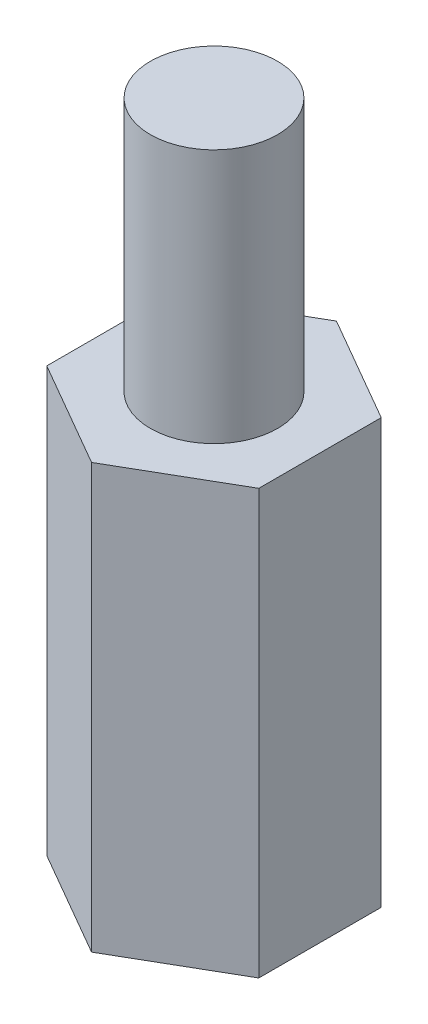
SolidWorks part; units mm, degrees
material "1023 Carbon Steel Sheet (SS)"
ref_plane "Front Plane" through (0, 0, 0) normal (0, 0, 1) x (1, 0, 0)
ref_plane "Top Plane" through (0, 0, 0) normal (0, 1, 0) x (1, 0, 0)
ref_plane "Right Plane" through (0, 0, 0) normal (1, 0, 0) x (0, 0, -1)
sketch "Sketch1" plane through (0, 0, 0) normal (0, 1, 0) x (1, 0, 0)
  line L1 (2.5, 1.4434) -> (0, 2.8868)
  line L2 (0, 2.8868) -> (-2.5, 1.4434)
  line L3 (-2.5, 1.4434) -> (-2.5, -1.4434)
  line L4 (-2.5, -1.4434) -> (0, -2.8868)
  line L5 (0, -2.8868) -> (2.5, -1.4434)
  line L6 (2.5, -1.4434) -> (2.5, 1.4434)
  circle A0 centre (0, 0) radius 2.5 construction
  dimension "D1" = 5
extrude "Boss-Extrude1" add sketch "Sketch1" along normal blind 16
sketch "Sketch2" plane through (0, 0, 0) normal (0, 1, 0) x (1, 0, 0)
  circle A0 centre (0, 0) radius 1.5025
  dimension "D1" = 3.005
extrude "Cut-Extrude1" cut sketch "Sketch2" along normal blind 6.005
sketch "Sketch3" plane through (0, 16, 0) normal (0, 1, 0) x (1, 0, 0)
  line L1 (0, 2.8868) -> (-2.5, 1.4434)
  line L2 (-2.5, 1.4434) -> (-2.5, -1.4434)
  line L3 (-2.5, -1.4434) -> (0, -2.8868)
  line L4 (0, -2.8868) -> (2.5, -1.4434)
  line L5 (2.5, -1.4434) -> (2.5, 1.4434)
  line L6 (2.5, 1.4434) -> (0, 2.8868)
  circle A0 centre (0, 0) radius 1.5
  circle A1 centre (0, 0) radius 2.5 construction
  dimension "D1" = 3
extrude "Cut-Extrude2" cut sketch "Sketch3" against normal blind 6
